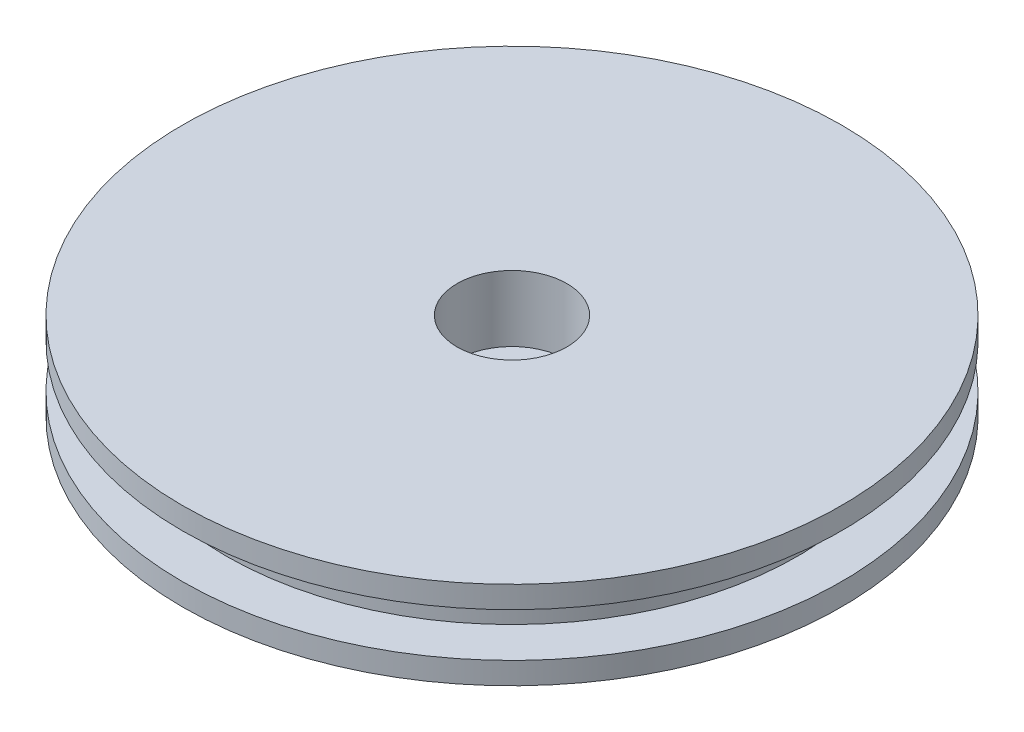
SolidWorks part; units mm, degrees
ref_plane "Plan de face" through (0, 0, 0) normal (0, 0, 1) x (1, 0, 0)
ref_plane "Plan de dessus" through (0, 0, 0) normal (0, 1, 0) x (1, 0, 0)
ref_plane "Plan de droite" through (0, 0, 0) normal (1, 0, 0) x (0, 0, -1)
sketch "Esquisse1" plane through (0, 0, 0) normal (1, 0, 0) x (0, 0, -1)
  line L0 (0, 2) -> (0, -10.5666) construction
  line L1 (0, 0) -> (-22.3271, 0) construction
  line L2 (0, 2) -> (-15, 2)
  line L3 (-15, 2) -> (-15, 1)
  line L4 (-15, 1) -> (-13, 1)
  line L5 (-13, 1) -> (-13, -1)
  line L6 (0, 2) -> (0, -2)
  line L8 (-15, -1) -> (-13, -1)
  line L9 (-15, -2) -> (-15, -1)
  line L10 (0, -2) -> (-15, -2)
  point P11 (-13, 0)
  dimension "D1" = 15
  dimension "D2" = 2
  dimension "D3" = 1
  dimension "D4" = 1
revolve "Révolution1" add sketch "Esquisse1" angle 360 about L0
ref_point "Point1"
hole_wizard "Perçage1" positions "Esquisse3" profile "Esquisse4" legacy end condition through all
sketch "Esquisse3" plane through (0, 2, 0) normal (0, 1, 0) x (1, 0, 0)
  point P0 (0, 0)
sketch "Esquisse4" plane through (0, 2, 0) normal (1, 0, 0) x (0, 0, 1)
  line L0 (0, 0) -> (0, 4)
  line L1 (0, 4) -> (1.5, 4)
  line L2 (1.5, 4) -> (1.5, 3)
  line L3 (1.5, 3) -> (2.5, 3)
  line L4 (2.5, 3) -> (2.5, 0)
  line L5 (2.5, 0) -> (0, 0)
  line L6 (0, 110) -> (0, -10) construction
  dimension "Diamètre" = 3
  dimension "Profondeur" = 4
  dimension "Diamètre chambrage" = 5
  dimension "Profondeur chambrage" = 3
